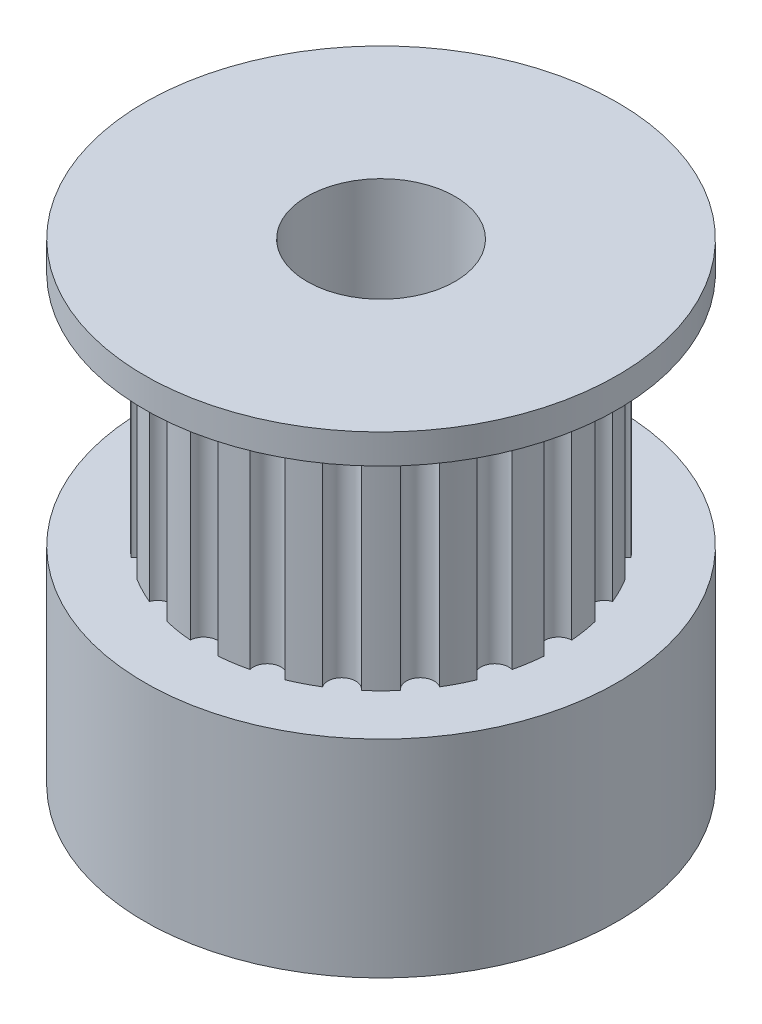
SolidWorks part; units mm, degrees
ref_plane "Plan de face" through (0, 0, 0) normal (0, 0, 1) x (1, 0, 0)
ref_plane "Plan de dessus" through (0, 0, 0) normal (0, 1, 0) x (1, 0, 0)
ref_plane "Plan de droite" through (0, 0, 0) normal (1, 0, 0) x (0, 0, -1)
sketch "Esquisse1" plane through (0, 0, 0) normal (0, 0, 1) x (1, 0, 0)
  line L0 (0, 0) -> (0, 16)
  line L1 (0, 16) -> (8, 16)
  line L2 (0, 0) -> (8, 0)
  line L3 (8, 0) -> (8, 7)
  line L4 (8, 16) -> (8, 15)
  line L5 (8, 15) -> (6, 15)
  line L6 (6, 15) -> (6, 7)
  line L7 (6, 7) -> (8, 7)
  dimension "D1" = 16
  dimension "D2" = 8
  dimension "D3" = 7
  dimension "D4" = 1
  dimension "D5" = 2
revolve "Révolution1" add sketch "Esquisse1" angle 360 about L0
sketch "Esquisse2" plane through (0, 16, 0) normal (0, 1, 0) x (1, 0, 0)
  circle A0 centre (0, 0) radius 2.5
  dimension "D1" = 5
extrude "Enlèv. mat.-Extru.1" cut sketch "Esquisse2" against normal through all
sketch "Esquisse3" plane through (0, 15, 0) normal (0, -1, 0) x (1, 0, 0)
  line L0 (5.9815, -0.4708) -> (5.9815, 0.4708) construction
  line L1 (5.8342, -1.4007) -> (5.9815, -0.4708) construction
  arc A0 (5.9815, -0.4708) -> (5.9815, 0.4708) centre (6, 0) cw
  circle A1 centre (0, 0) radius 6 construction
  arc A2 (5.5433, -2.2961) -> (5.8342, -1.4007) centre (0, 0) ccw
  arc A3 (5.5433, -2.2961) -> (5.8342, -1.4007) centre (5.7063, -1.8541) cw
  arc A4 (4.5624, -3.8967) -> (5.1158, -3.135) centre (4.8541, -3.5267) cw
  arc A5 (3.135, -5.1158) -> (3.8967, -4.5624) centre (3.5267, -4.8541) cw
  arc A6 (1.4007, -5.8342) -> (2.2961, -5.5433) centre (1.8541, -5.7063) cw
  arc A7 (-0.4708, -5.9815) -> (0.4708, -5.9815) centre (0, -6) cw
  arc A8 (-2.2961, -5.5433) -> (-1.4007, -5.8342) centre (-1.8541, -5.7063) cw
  arc A9 (-3.8967, -4.5624) -> (-3.135, -5.1158) centre (-3.5267, -4.8541) cw
  arc A10 (-5.1158, -3.135) -> (-4.5624, -3.8967) centre (-4.8541, -3.5267) cw
  arc A11 (-5.8342, -1.4007) -> (-5.5433, -2.2961) centre (-5.7063, -1.8541) cw
  arc A12 (-5.9815, 0.4708) -> (-5.9815, -0.4708) centre (-6, 0) cw
  arc A13 (-5.5433, 2.2961) -> (-5.8342, 1.4007) centre (-5.7063, 1.8541) cw
  arc A14 (-4.5624, 3.8967) -> (-5.1158, 3.135) centre (-4.8541, 3.5267) cw
  arc A15 (-3.135, 5.1158) -> (-3.8967, 4.5624) centre (-3.5267, 4.8541) cw
  arc A16 (-1.4007, 5.8342) -> (-2.2961, 5.5433) centre (-1.8541, 5.7063) cw
  arc A17 (0.4708, 5.9815) -> (-0.4708, 5.9815) centre (0, 6) cw
  arc A18 (2.2961, 5.5433) -> (1.4007, 5.8342) centre (1.8541, 5.7063) cw
  arc A19 (3.8967, 4.5624) -> (3.135, 5.1158) centre (3.5267, 4.8541) cw
  arc A20 (5.1158, 3.135) -> (4.5624, 3.8967) centre (4.8541, 3.5267) cw
  arc A21 (5.8342, 1.4007) -> (5.5433, 2.2961) centre (5.7063, 1.8541) cw
  arc A22 (5.9815, -0.4708) -> (5.9815, 0.4708) centre (0, 0) ccw
  arc A23 (5.8342, 1.4007) -> (5.5433, 2.2961) centre (0, 0) ccw
  arc A24 (5.1158, 3.135) -> (4.5624, 3.8967) centre (0, 0) ccw
  arc A25 (3.8967, 4.5624) -> (3.135, 5.1158) centre (0, 0) ccw
  arc A26 (2.2961, 5.5433) -> (1.4007, 5.8342) centre (0, 0) ccw
  arc A27 (0.4708, 5.9815) -> (-0.4708, 5.9815) centre (0, 0) ccw
  arc A28 (-1.4007, 5.8342) -> (-2.2961, 5.5433) centre (0, 0) ccw
  arc A29 (-3.135, 5.1158) -> (-3.8967, 4.5624) centre (0, 0) ccw
  arc A30 (-4.5624, 3.8967) -> (-5.1158, 3.135) centre (0, 0) ccw
  arc A31 (-5.5433, 2.2961) -> (-5.8342, 1.4007) centre (0, 0) ccw
  arc A32 (-5.9815, 0.4708) -> (-5.9815, -0.4708) centre (0, 0) ccw
  arc A33 (-5.8342, -1.4007) -> (-5.5433, -2.2961) centre (0, 0) ccw
  arc A34 (-5.1158, -3.135) -> (-4.5624, -3.8967) centre (0, 0) ccw
  arc A35 (-3.8967, -4.5624) -> (-3.135, -5.1158) centre (0, 0) ccw
  arc A36 (-2.2961, -5.5433) -> (-1.4007, -5.8342) centre (0, 0) ccw
  arc A37 (-0.4708, -5.9815) -> (0.4708, -5.9815) centre (0, 0) ccw
  arc A38 (1.4007, -5.8342) -> (2.2961, -5.5433) centre (0, 0) ccw
  arc A39 (3.135, -5.1158) -> (3.8967, -4.5624) centre (0, 0) ccw
  arc A40 (4.5624, -3.8967) -> (5.1158, -3.135) centre (0, 0) ccw
  point P10 (0, 0)
  point P67 (0, 0)
  dimension "D1" = 20
extrude "Enlèv. mat.-Extru.2" cut sketch "Esquisse3" along normal up to surface (8 mm away) up to face at (0, 7, -6)
